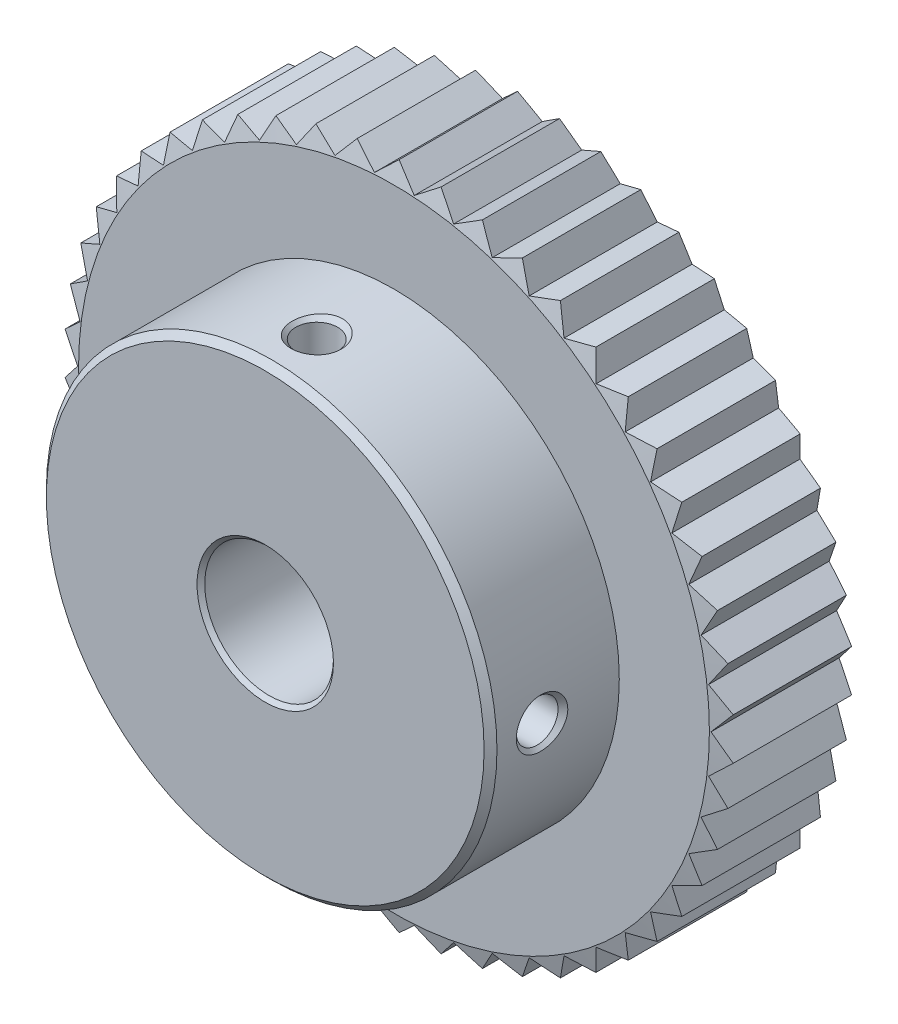
SolidWorks part; units mm, degrees
ref_plane "Front Plane" through (0, 0, 0) normal (0, 0, 1) x (1, 0, 0)
ref_plane "Top Plane" through (0, 0, 0) normal (0, 1, 0) x (1, 0, 0)
ref_plane "Right Plane" through (0, 0, 0) normal (1, 0, 0) x (0, 0, -1)
ref_plane "Plane1" through (0, 0, 0) normal (1, 0, 0) x (0, 0, -1)
sketch "Sketch1" plane through (0, 0, 0) normal (1, 0, 0) x (0, 0, -1)
  line L0 (-20, 5.3) -> (-19.7, 5)
  line L1 (-19.7, 5) -> (-0.3, 5)
  line L2 (-0.3, 5) -> (0, 5.3)
  line L3 (0, 5.3) -> (0, 24.5)
  line L4 (0, 24.5) -> (-0.6699, 27)
  line L5 (-0.6699, 27) -> (-9.3301, 27)
  line L6 (-9.3301, 27) -> (-10, 24.5)
  line L7 (-10, 24.5) -> (-10, 17.5)
  line L8 (-10, 17.5) -> (-19.5, 17.5)
  line L9 (-19.5, 17.5) -> (-20, 17)
  line L10 (-20, 17) -> (-20, 5.3)
  line L11 (0, 0) -> (-20, 0) construction
revolve "Revolve1" add sketch "Sketch1" angle 360 about L11
ref_plane "Plane2" through (0, 0, 0) normal (0, 0, 1) x (1, 0, 0)
sketch "Sketch2" plane through (0, 0, 0) normal (0, 0, 1) x (1, 0, 0)
  line L0 (-25.9487, -1.6326) -> (-24.406, -3.0832)
  line L1 (-24.406, -3.0832) -> (-25.5395, -4.8719)
  line L2 (-25.5395, -4.8719) -> (-23.8271, -6.1178)
  line L3 (-23.8271, -6.1178) -> (-24.7275, -8.0344)
  line L4 (-24.7275, -8.0344) -> (-22.8725, -9.0559)
  line L5 (-22.8725, -9.0559) -> (-23.5255, -11.0703)
  line L6 (-23.5255, -11.0703) -> (-21.5571, -11.8511)
  line L7 (-21.5571, -11.8511) -> (-21.9525, -13.9315)
  line L8 (-21.9525, -13.9315) -> (-19.9018, -14.4595)
  line L9 (-19.9018, -14.4595) -> (-20.0333, -16.573)
  line L10 (-20.0333, -16.573) -> (-17.9326, -16.8399)
  line L11 (-17.9326, -16.8399) -> (-17.7982, -18.9532)
  line L12 (-17.7982, -18.9532) -> (-15.6806, -18.9546)
  line L13 (-15.6806, -18.9546) -> (-15.2824, -21.0344)
  line L14 (-15.2824, -21.0344) -> (-13.1813, -20.7705)
  line L15 (-13.1813, -20.7705) -> (-12.5256, -22.784)
  line L16 (-12.5256, -22.784) -> (-10.4742, -22.2587)
  line L17 (-10.4742, -22.2587) -> (-9.5712, -24.1742)
  line L18 (-9.5712, -24.1742) -> (-7.6018, -23.396)
  line L19 (-7.6018, -23.396) -> (-6.4659, -25.1832)
  line L20 (-6.4659, -25.1832) -> (-4.6096, -24.1643)
  line L21 (-4.6096, -24.1643) -> (-3.2587, -25.795)
  line L22 (-3.2587, -25.795) -> (-1.5446, -24.5515)
  line L23 (-1.5446, -24.5515) -> (0, -26)
  line L24 (0, -26) -> (1.5446, -24.5515)
  line L25 (1.5446, -24.5515) -> (3.2587, -25.795)
  line L26 (3.2587, -25.795) -> (4.6096, -24.1643)
  line L27 (4.6096, -24.1643) -> (6.4659, -25.1832)
  line L28 (6.4659, -25.1832) -> (7.6018, -23.396)
  line L29 (7.6018, -23.396) -> (9.5712, -24.1742)
  line L30 (9.5712, -24.1742) -> (10.4742, -22.2587)
  line L31 (10.4742, -22.2587) -> (12.5256, -22.784)
  line L32 (12.5256, -22.784) -> (13.1813, -20.7705)
  line L33 (13.1813, -20.7705) -> (15.2824, -21.0344)
  line L34 (15.2824, -21.0344) -> (15.6806, -18.9546)
  line L35 (15.6806, -18.9546) -> (17.7982, -18.9532)
  line L36 (17.7982, -18.9532) -> (17.9326, -16.8399)
  line L37 (17.9326, -16.8399) -> (20.0333, -16.573)
  line L38 (20.0333, -16.573) -> (19.9018, -14.4595)
  line L39 (19.9018, -14.4595) -> (21.9525, -13.9315)
  line L40 (21.9525, -13.9315) -> (21.5571, -11.8511)
  line L41 (21.5571, -11.8511) -> (23.5255, -11.0703)
  line L42 (23.5255, -11.0703) -> (22.8725, -9.0559)
  line L43 (22.8725, -9.0559) -> (24.7275, -8.0344)
  line L44 (24.7275, -8.0344) -> (23.8271, -6.1178)
  line L45 (23.8271, -6.1178) -> (25.5395, -4.8719)
  line L46 (25.5395, -4.8719) -> (24.406, -3.0832)
  line L47 (24.406, -3.0832) -> (25.9487, -1.6326)
  line L48 (25.9487, -1.6326) -> (24.6, 0)
  line L49 (24.6, 0) -> (25.9487, 1.6326)
  line L50 (25.9487, 1.6326) -> (24.406, 3.0832)
  line L51 (24.406, 3.0832) -> (25.5395, 4.8719)
  line L52 (25.5395, 4.8719) -> (23.8271, 6.1178)
  line L53 (23.8271, 6.1178) -> (24.7275, 8.0344)
  line L54 (24.7275, 8.0344) -> (22.8725, 9.0559)
  line L55 (22.8725, 9.0559) -> (23.5255, 11.0703)
  line L56 (23.5255, 11.0703) -> (21.5571, 11.8511)
  line L57 (21.5571, 11.8511) -> (21.9525, 13.9315)
  line L58 (21.9525, 13.9315) -> (19.9018, 14.4595)
  line L59 (19.9018, 14.4595) -> (20.0333, 16.573)
  line L60 (20.0333, 16.573) -> (17.9326, 16.8399)
  line L61 (17.9326, 16.8399) -> (17.7982, 18.9532)
  line L62 (17.7982, 18.9532) -> (15.6806, 18.9546)
  line L63 (15.6806, 18.9546) -> (15.2824, 21.0344)
  line L64 (15.2824, 21.0344) -> (13.1813, 20.7705)
  line L65 (13.1813, 20.7705) -> (12.5256, 22.784)
  line L66 (12.5256, 22.784) -> (10.4742, 22.2587)
  line L67 (10.4742, 22.2587) -> (9.5712, 24.1742)
  line L68 (9.5712, 24.1742) -> (7.6018, 23.396)
  line L69 (7.6018, 23.396) -> (6.4659, 25.1832)
  line L70 (6.4659, 25.1832) -> (4.6096, 24.1643)
  line L71 (4.6096, 24.1643) -> (3.2587, 25.795)
  line L72 (3.2587, 25.795) -> (1.5446, 24.5515)
  line L73 (1.5446, 24.5515) -> (0, 26)
  line L74 (0, 26) -> (-1.5446, 24.5515)
  line L75 (-1.5446, 24.5515) -> (-3.2587, 25.795)
  line L76 (-3.2587, 25.795) -> (-4.6096, 24.1643)
  line L77 (-4.6096, 24.1643) -> (-6.4659, 25.1832)
  line L78 (-6.4659, 25.1832) -> (-7.6018, 23.396)
  line L79 (-7.6018, 23.396) -> (-9.5712, 24.1742)
  line L80 (-9.5712, 24.1742) -> (-10.4742, 22.2587)
  line L81 (-10.4742, 22.2587) -> (-12.5256, 22.784)
  line L82 (-12.5256, 22.784) -> (-13.1813, 20.7705)
  line L83 (-13.1813, 20.7705) -> (-15.2824, 21.0344)
  line L84 (-15.2824, 21.0344) -> (-15.6806, 18.9546)
  line L85 (-15.6806, 18.9546) -> (-17.7982, 18.9532)
  line L86 (-17.7982, 18.9532) -> (-17.9326, 16.8399)
  line L87 (-17.9326, 16.8399) -> (-20.0333, 16.573)
  line L88 (-20.0333, 16.573) -> (-19.9018, 14.4595)
  line L89 (-19.9018, 14.4595) -> (-21.9525, 13.9315)
  line L90 (-21.9525, 13.9315) -> (-21.5571, 11.8511)
  line L91 (-21.5571, 11.8511) -> (-23.5255, 11.0703)
  line L92 (-23.5255, 11.0703) -> (-22.8725, 9.0559)
  line L93 (-22.8725, 9.0559) -> (-24.7275, 8.0344)
  line L94 (-24.7275, 8.0344) -> (-23.8271, 6.1178)
  line L95 (-23.8271, 6.1178) -> (-25.5395, 4.8719)
  line L96 (-25.5395, 4.8719) -> (-24.406, 3.0832)
  line L97 (-24.406, 3.0832) -> (-25.9487, 1.6326)
  line L98 (-25.9487, 1.6326) -> (-24.6, 0)
  line L99 (-24.6, 0) -> (-25.9487, -1.6326)
  circle A0 centre (0, 0) radius 52
extrude "Cut-Extrude1" cut sketch "Sketch2" along normal blind 10
ref_plane "Plane3" through (0, 0, 16) normal (0, 0, 1) x (1, 0, 0)
sketch "Sketch3" plane through (0, 0, 16) normal (0, 0, 1) x (1, 0, 0)
  line L0 (0, 0) -> (-2, 0)
  line L1 (-2, 0) -> (-2, 5)
  line L2 (-2, 5) -> (-1.621, 5.379)
  line L3 (-1.621, 5.379) -> (-1.621, 17.121)
  line L4 (-1.621, 17.121) -> (-2, 17.5)
  line L5 (-2, 17.5) -> (-2, 27.5)
  line L6 (-2, 27.5) -> (0, 27.5)
  line L7 (0, 27.5) -> (0, 0)
  line L8 (0, 27.5) -> (0, 0) construction
revolve "Cut-Revolve1" cut sketch "Sketch3" angle 360 about L8
ref_plane "Plane4" through (0, 0, 16) normal (0, 0, 1) x (1, 0, 0)
sketch "Sketch4" plane through (0, 0, 16) normal (0, 0, 1) x (1, 0, 0)
  line L0 (0, 0) -> (0, 2)
  line L1 (0, 2) -> (5, 2)
  line L2 (5, 2) -> (5.379, 1.621)
  line L3 (5.379, 1.621) -> (17.121, 1.621)
  line L4 (17.121, 1.621) -> (17.5, 2)
  line L5 (17.5, 2) -> (27.5, 2)
  line L6 (27.5, 2) -> (27.5, 0)
  line L7 (27.5, 0) -> (0, 0)
  line L8 (27.5, 0) -> (0, 0) construction
revolve "Cut-Revolve2" cut sketch "Sketch4" angle 360 about L8
